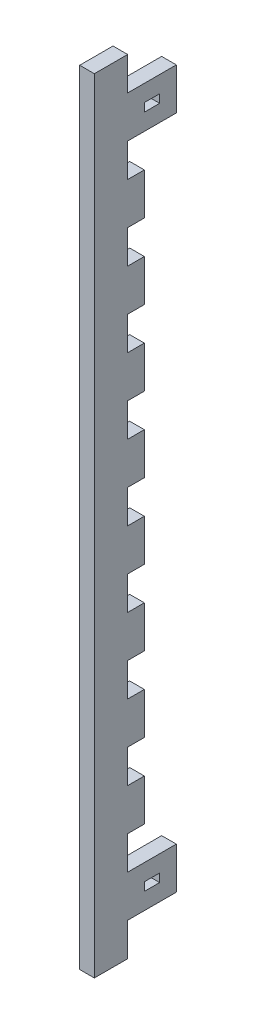
SolidWorks part; units mm, degrees
material "Acrylic (Medium-high impact)"
ref_plane "Front" through (0, 0, 0) normal (0, 0, 1) x (1, 0, 0)
ref_plane "Top" through (0, 0, 0) normal (0, 1, 0) x (1, 0, 0)
ref_plane "Right" through (0, 0, 0) normal (1, 0, 0) x (0, 0, -1)
sketch "Sketch1" plane through (0, 0, 0) normal (1, 0, 0) x (0, 0, -1)
  line L0 (9.525, 120.65) -> (9.525, 107.95)
  line L1 (-9.525, 149.225) -> (9.525, 149.225)
  line L2 (-9.525, 149.225) -> (-9.525, -149.225)
  line L3 (-9.525, -149.225) -> (9.525, -149.225)
  line L4 (9.525, 149.225) -> (9.525, -149.225)
  line L17 (9.525, 149.225) -> (3.175, 149.225)
  line L22 (9.525, 149.225) -> (9.525, 136.525)
  line L27 (9.525, 136.525) -> (3.175, 136.525)
  line L32 (3.175, 149.225) -> (3.175, 136.525)
  line L37 (9.525, 120.65) -> (3.175, 120.65)
  line L42 (3.175, 120.65) -> (3.175, 107.95)
  line L47 (9.525, 107.95) -> (3.175, 107.95)
  line L52 (9.525, 92.075) -> (9.525, 79.375)
  line L57 (9.525, 92.075) -> (3.175, 92.075)
  line L62 (3.175, 92.075) -> (3.175, 79.375)
  line L67 (9.525, 79.375) -> (3.175, 79.375)
  line L68 (9.525, 63.5) -> (9.525, 50.8)
  line L72 (9.525, 63.5) -> (3.175, 63.5)
  line L73 (3.175, 63.5) -> (3.175, 50.8)
  line L78 (9.525, 50.8) -> (3.175, 50.8)
  line L79 (9.525, 34.925) -> (9.525, 22.225)
  line L80 (9.525, 34.925) -> (3.175, 34.925)
  line L81 (3.175, 34.925) -> (3.175, 22.225)
  line L82 (9.525, 22.225) -> (3.175, 22.225)
  line L83 (9.525, 6.35) -> (9.525, -6.35)
  line L84 (9.525, 6.35) -> (3.175, 6.35)
  line L85 (3.175, 6.35) -> (3.175, -6.35)
  line L86 (9.525, -6.35) -> (3.175, -6.35)
  line L87 (9.525, -22.225) -> (9.525, -34.925)
  line L88 (9.525, -22.225) -> (3.175, -22.225)
  line L89 (3.175, -22.225) -> (3.175, -34.925)
  line L90 (9.525, -34.925) -> (3.175, -34.925)
  line L91 (9.525, -50.8) -> (9.525, -63.5)
  line L92 (9.525, -50.8) -> (3.175, -50.8)
  line L93 (3.175, -50.8) -> (3.175, -63.5)
  line L94 (9.525, -63.5) -> (3.175, -63.5)
  line L95 (9.525, -79.375) -> (9.525, -92.075)
  line L96 (9.525, -79.375) -> (3.175, -79.375)
  line L97 (3.175, -79.375) -> (3.175, -92.075)
  line L98 (9.525, -92.075) -> (3.175, -92.075)
  line L99 (9.525, -107.95) -> (9.525, -120.65)
  line L100 (9.525, -107.95) -> (3.175, -107.95)
  line L101 (3.175, -107.95) -> (3.175, -120.65)
  line L102 (9.525, -120.65) -> (3.175, -120.65)
  line L103 (9.525, -136.525) -> (9.525, -149.225)
  line L104 (9.525, -136.525) -> (3.175, -136.525)
  line L105 (3.175, -136.525) -> (3.175, -149.225)
  line L106 (9.525, -149.225) -> (3.175, -149.225)
  point P4 (0, -149.225)
  point P6 (-9.525, 0)
  dimension "D1" = 19.05
  dimension "D2" = 298.45
  dimension "D3" = 12.7
  dimension "D4" = 6.35
  dimension "D5" = 11
extrude "Boss-Extrude1" add sketch "Sketch1" along normal blind 5.588
sketch "Sketch2" plane through (5.588, 0, 0) normal (1, 0, 0) x (0, 0, -1)
  line L5 (9.525, -136.525) -> (3.175, -136.525) construction
  line L6 (9.525, -120.65) -> (21.717, -120.65)
  line L7 (9.525, -120.65) -> (9.525, -136.525)
  line L8 (9.525, -136.525) -> (21.717, -136.525)
  line L9 (21.717, -120.65) -> (21.717, -136.525)
  line L11 (9.525, -127) -> (15.367, -127)
  line L12 (9.525, -127) -> (9.525, -130.175)
  line L13 (9.525, -130.175) -> (15.367, -130.175)
  line L14 (15.367, -127) -> (15.367, -130.175)
  line L23 (9.525, 136.525) -> (21.717, 136.525)
  line L24 (9.525, 136.525) -> (9.525, 120.65)
  line L25 (9.525, 120.65) -> (21.717, 120.65)
  line L26 (21.717, 136.525) -> (21.717, 120.65)
  line L27 (9.525, 130.175) -> (15.367, 130.175)
  line L28 (9.525, 130.175) -> (9.525, 127)
  line L29 (9.525, 127) -> (15.367, 127)
  line L30 (15.367, 130.175) -> (15.367, 127)
  point P15 (15.367, 128.5875)
  point P17 (21.717, 128.5875)
  point P22 (15.367, -128.5875)
  point P27 (21.717, -128.5875)
  dimension "D1" = 12.192
  dimension "D3" = 3.175
  dimension "D4" = 5.842
extrude "Boss-Extrude2" add sketch "Sketch2" against normal up to surface (5.588 mm away) up to face at (0, 0, -5.4841)
